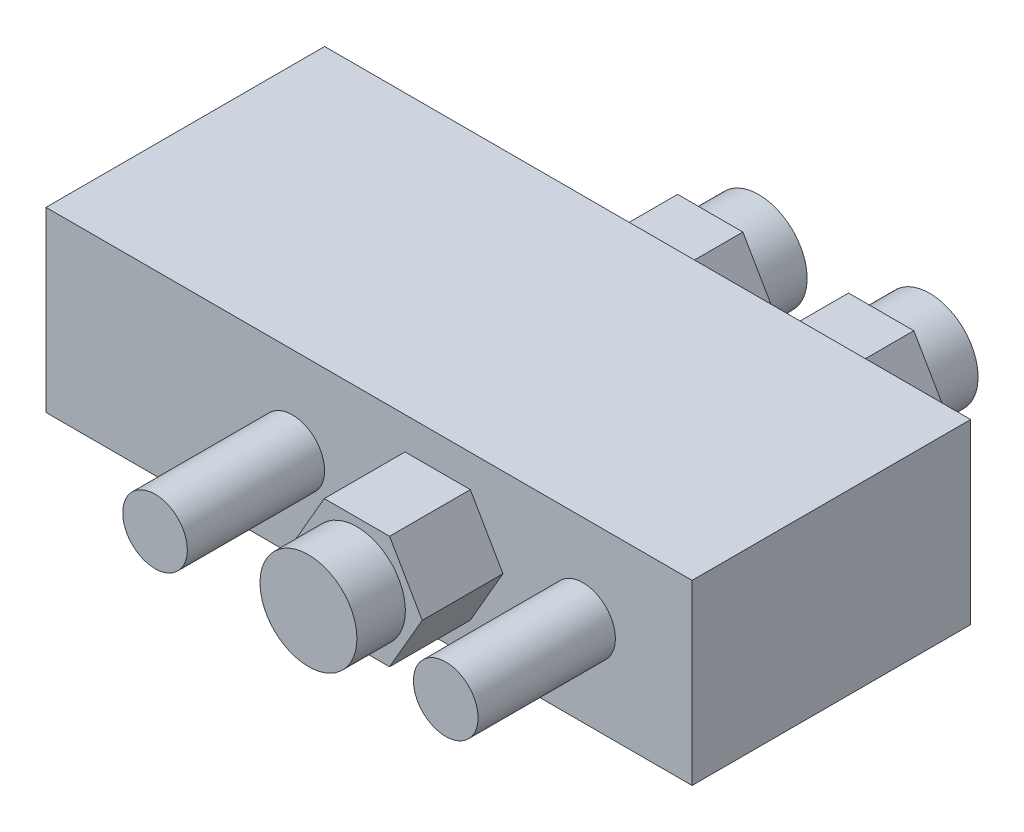
SolidWorks part; units mm, degrees
ref_plane "Front Plane" through (0, 0, 0) normal (0, 0, 1) x (1, 0, 0)
ref_plane "Top Plane" through (0, 0, 0) normal (0, 1, 0) x (1, 0, 0)
ref_plane "Right Plane" through (0, 0, 0) normal (1, 0, 0) x (0, 0, -1)
sketch "Sketch1" plane through (0, 0, 0) normal (0, 1, 0) x (1, 0, 0)
  line L0 (0, 0) -> (80, 0)
  line L1 (80, 0) -> (80, 34.5)
  line L3 (0, 34.5) -> (0, 0)
  line L41 (80, 34.5) -> (0, 34.5)
  point P4 (0, 34.144)
  dimension "D1" = 80
  dimension "D2" = 34.5
extrude "Boss-Extrude1" add sketch "Sketch1" along normal blind 22
sketch "Sketch2" plane through (0, 0, 0) normal (0, 0, 1) x (1, 0, 0)
  line L0 (0, 22) -> (0, 0) construction
  line L2 (80, 22) -> (80, 0) construction
  circle A0 centre (30.5, 11) radius 4
  circle A2 centre (66.5, 11) radius 4
  point P7 (0, 11)
  dimension "D1" = 8
  dimension "D2" = 28
  dimension "D3" = 9.5
extrude "Boss-Extrude2" add sketch "Sketch2" along normal blind 17
sketch "Sketch3" plane through (0, 0, -34.5) normal (0, 0, -1) x (-1, 0, 0)
  line L0 (-80, 22) -> (-80, 0) construction
  line L1 (-50.8342, 11) -> (-54.8756, 18)
  line L2 (-54.8756, 18) -> (-62.9585, 18)
  line L3 (-62.9585, 18) -> (-67, 11)
  line L4 (-67, 11) -> (-62.9585, 4)
  line L5 (-62.9585, 4) -> (-54.8756, 4)
  line L6 (-54.8756, 4) -> (-50.8342, 11)
  line L7 (-29.6684, 11) -> (-33.7098, 18)
  line L8 (-33.7098, 18) -> (-41.7927, 18)
  line L9 (-41.7927, 18) -> (-45.8342, 11)
  line L10 (-45.8342, 11) -> (-41.7927, 4)
  line L11 (-41.7927, 4) -> (-33.7098, 4)
  line L12 (-33.7098, 4) -> (-29.6684, 11)
  line L13 (-80, 0) -> (0, 0) construction
  circle A2 centre (-58.9171, 11) radius 7 construction
  circle A3 centre (-37.7513, 11) radius 7 construction
  point P19 (-80, 11)
  dimension "D1" = 14
  dimension "D2" = 13
  dimension "D3" = 5
extrude "Boss-Extrude3" add sketch "Sketch3" along normal blind 10
sketch "Sketch6" plane through (0, 0, 0) normal (0, 0, 1) x (1, 0, 0)
  line L0 (80, 22) -> (80, 0) construction
  line L1 (56.5829, 11) -> (52.5415, 18)
  line L2 (52.5415, 18) -> (44.4585, 18)
  line L3 (44.4585, 18) -> (40.4171, 11)
  line L4 (40.4171, 11) -> (44.4585, 4)
  line L5 (44.4585, 4) -> (52.5415, 4)
  line L6 (52.5415, 4) -> (56.5829, 11)
  line L7 (0, 22) -> (80, 22) construction
  line L8 (30.5, 11) -> (66.5, 11) construction
  circle A0 centre (48.5, 11) radius 7 construction
  point P1 (48.5, 11)
  point P11 (80, 11)
  dimension "D1" = 14
extrude "Boss-Extrude6" add sketch "Sketch6" along normal blind 10
sketch "Sketch7" plane through (0, 0, 10) normal (0, 0, 1) x (1, 0, 0)
  line L0 (44.4585, 4) -> (52.5415, 18) construction
  line L2 (56.5829, 11) -> (52.5415, 18) construction
  circle A0 centre (48.5, 11) radius 6
  dimension "D1" = 1
extrude "Boss-Extrude7" add sketch "Sketch7" along normal blind 6
sketch "Sketch8" plane through (0, 0, -44.5) normal (0, 0, -1) x (-1, 0, 0)
  line L0 (-67, 11) -> (-50.8342, 11) construction
  line L1 (-45.8342, 11) -> (-29.6684, 11) construction
  line L3 (-50.8342, 11) -> (-54.8756, 18) construction
  circle A0 centre (-58.9171, 11) radius 6
  circle A1 centre (-37.7513, 11) radius 6
  dimension "D1" = 1
extrude "Boss-Extrude8" add sketch "Sketch8" along normal blind 6
